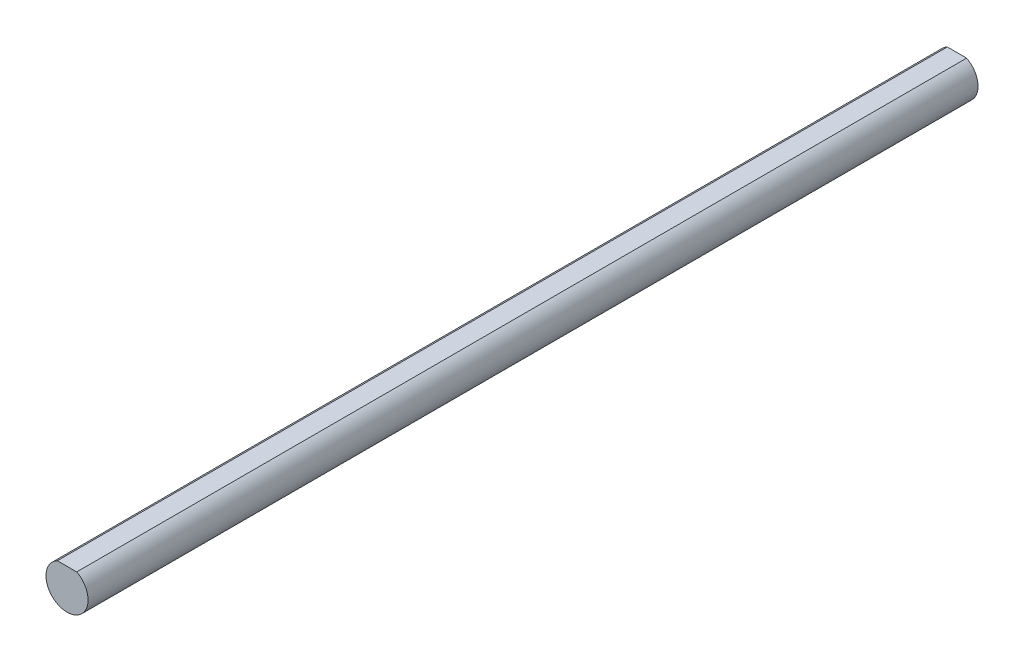
SolidWorks part; units mm, degrees
material "Alloy Steel"
ref_plane "Front Plane" through (0, 0, 0) normal (0, 0, 1) x (1, 0, 0)
ref_plane "Top Plane" through (0, 0, 0) normal (0, 1, 0) x (1, 0, 0)
ref_plane "Right Plane" through (0, 0, 0) normal (1, 0, 0) x (0, 0, -1)
ref_plane "Plane1" through (0, 0, 50) normal (0, 0, 1) x (1, 0, 0)
sketch "Sketch1" plane through (0, 0, 50) normal (0, 0, 1) x (1, 0, 0)
  line L0 (1.0878, 2.1) -> (-1.0878, 2.1)
  arc A0 (-1.0878, 2.1) -> (1.0878, 2.1) centre (0, 0) ccw
extrude "Boss-Extrude1" add sketch "Sketch1" against normal blind 100
